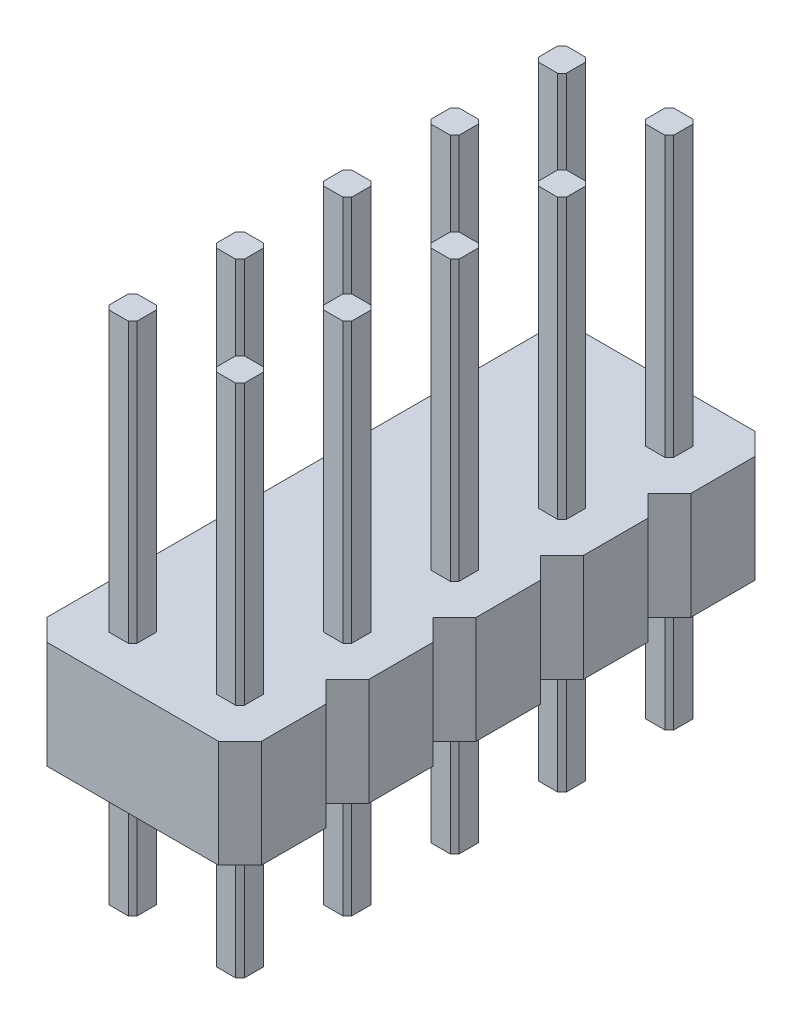
SolidWorks part; units mm, degrees
ref_plane "Front Plane" through (0, 0, 0) normal (0, 0, 1) x (1, 0, 0)
ref_plane "Top Plane" through (0, 0, 0) normal (0, 1, 0) x (1, 0, 0)
ref_plane "Right Plane" through (0, 0, 0) normal (1, 0, 0) x (0, 0, -1)
sketch "Sketch1" plane through (0, 0, 0) normal (0, 1, 0) x (1, 0, 0)
  line L0 (-0.325, 0.225) -> (-0.225, 0.325)
  line L1 (-0.225, -0.325) -> (0.225, -0.325)
  line L2 (-0.325, -0.225) -> (-0.325, 0.225)
  line L3 (-0.225, 0.325) -> (0.225, 0.325)
  line L4 (0.325, -0.225) -> (0.325, 0.225)
  line L5 (-0.325, -0.325) -> (0.325, 0.325) construction
  line L6 (-0.325, 0.325) -> (0.325, -0.325) construction
  line L7 (0.225, 0.325) -> (0.325, 0.225)
  line L8 (0.225, -0.325) -> (0.325, -0.225)
  line L9 (-0.325, -0.225) -> (-0.225, -0.325)
  point P0 (0, 0)
  dimension "D1" = 0.65
extrude "Boss-Extrude1" add sketch "Sketch1" along normal blind 12
pattern_linear "LPattern1" count 2 spacing 2.5 along (1, 0, 0) of bodies 101
ref_plane "Plane1" through (0, 3, 0) normal (0, -1, 0) x (-1, 0, 0)
sketch "Sketch3" plane through (0, 3, 0) normal (0, -1, 0) x (-1, 0, 0)
  line L0 (0.325, 0) -> (-2.825, 0) construction
  line L1 (0.325, 0.225) -> (0.325, -0.225) construction
  line L2 (-2.825, -0.225) -> (-2.825, 0.225) construction
  line L3 (-3.75, 0.75) -> (-3.25, 1.25)
  line L4 (-3.25, -1.25) -> (0.75, -1.25)
  line L5 (-3.75, -0.75) -> (-3.75, 0.75)
  line L6 (-3.25, 1.25) -> (0.75, 1.25)
  line L7 (1.25, -0.75) -> (1.25, 0.75)
  line L8 (-3.75, -1.25) -> (1.25, 1.25) construction
  line L9 (-3.75, 1.25) -> (1.25, -1.25) construction
  line L10 (0.75, 1.25) -> (1.25, 0.75)
  line L11 (0.75, -1.25) -> (1.25, -0.75)
  line L12 (-3.75, -0.75) -> (-3.25, -1.25)
  point P6 (-1.25, 0)
  dimension "D1" = 5
  dimension "D2" = 2.5
extrude "Boss-Extrude3" add sketch "Sketch3" against normal blind 2.5
pattern_linear "LPattern3" count 5 spacing 2.5 along (0, 0, 1) of bodies 104
combine bodies "Combine1" operation type add bodies to combine 104 109 110 111 112
